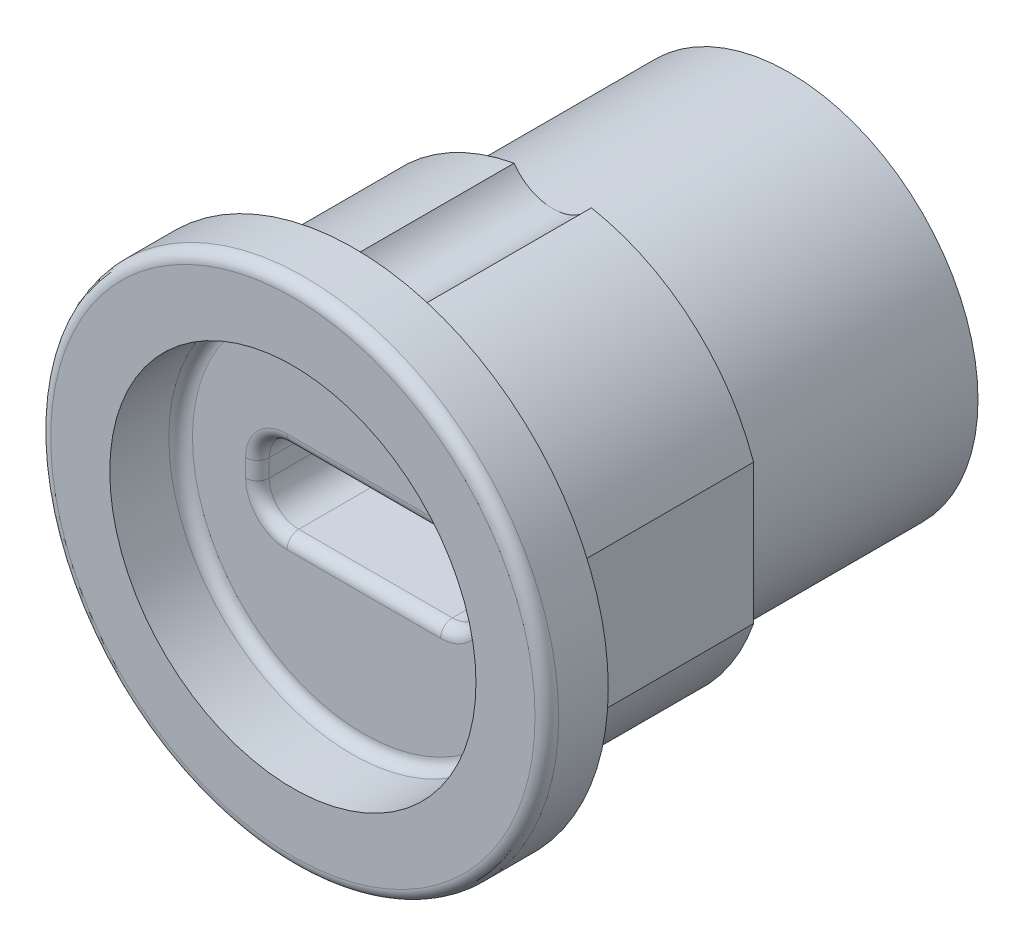
SolidWorks part; units mm, degrees
material "ABS"
ref_plane "Front Plane" through (0, 0, 0) normal (0, 0, 1) x (1, 0, 0)
ref_plane "Top Plane" through (0, 0, 0) normal (0, 1, 0) x (1, 0, 0)
ref_plane "Right Plane" through (0, 0, 0) normal (1, 0, 0) x (0, 0, -1)
sketch "Sketch1" plane through (0, 0, 0) normal (0, 0, 1) x (1, 0, 0)
  circle A0 centre (0, 0) radius 9
  dimension "D1" = 18
extrude "Boss-Extrude1" add sketch "Sketch1" against normal blind 18.4
sketch "Sketch2" plane through (0, 0, 0) normal (0, 0, 1) x (1, 0, 0)
  circle A0 centre (0, 0) radius 10.75
  dimension "D1" = 21.5
extrude "Boss-Extrude2" add sketch "Sketch2" along normal blind 2.6
sketch "Sketch3" plane through (0, 0, 2.6) normal (0, 0, 1) x (1, 0, 0)
  circle A0 centre (0, 0) radius 7.75
  dimension "D1" = 15.5
extrude "Cut-Extrude1" cut sketch "Sketch3" against normal blind 3
sketch "Sketch4" plane through (0, 0, -18.4) normal (0, 0, -1) x (-1, 0, 0)
  circle A0 centre (0, 0) radius 8
  circle A1 centre (0, 0) radius 9 construction
  circle A2 centre (0, 0) radius 9
  dimension "D1" = 16
extrude "Cut-Extrude2" cut sketch "Sketch4" against normal blind 10
sketch "Sketch5" plane through (0, 0, -8.4) normal (0, 0, -1) x (-1, 0, 0)
  line L0 (-8.5, 2.958) -> (-8.5, -2.958)
  line L1 (8.5, 2.958) -> (8.5, -2.958)
  circle A0 centre (0, 0) radius 9 construction
  arc A1 (-8.5, 2.958) -> (-8.5, -2.958) centre (0, 0) ccw
  arc A2 (8.5, 2.958) -> (-8.5, 2.958) centre (0, 0) ccw construction
  arc A3 (-8.5, -2.958) -> (8.5, -2.958) centre (0, 0) ccw construction
  arc A4 (8.5, -2.958) -> (8.5, 2.958) centre (0, 0) ccw
  arc A5 (-1.6363, 8.85) -> (1.6363, 8.85) centre (0, 10) ccw
  circle A6 centre (0, 0) radius 8 construction
  circle A7 centre (0, 0) radius 9 construction
  arc A8 (-1.6363, 8.85) -> (1.6363, 8.85) centre (0, 0) cw
  point P7 (-8.5, 0)
  point P9 (8.5, 0)
  point P11 (0, 8)
  dimension "D2" = 2
  dimension "D1" = 17
extrude "Cut-Extrude3" cut sketch "Sketch5" against normal up to surface (8.4 mm away) up to face at (9, 0, 0)
sketch "Sketch6" plane through (0, 0, 0) normal (0, 0, 1) x (1, 0, 0)
  line L1 (-3.25, 1.625) -> (3.25, 1.625)
  line L2 (-3.25, -1.625) -> (3.25, -1.625)
  line L7 (-4.5, -0.375) -> (-4.5, 0.375)
  line L8 (4.5, -0.375) -> (4.5, 0.375)
  arc A2 (-3.25, 1.625) -> (-4.5, 0.375) centre (-3.25, 0.375) ccw
  arc A3 (-4.5, -0.375) -> (-3.25, -1.625) centre (-3.25, -0.375) ccw
  arc A4 (3.25, -1.625) -> (4.5, -0.375) centre (3.25, -0.375) ccw
  arc A5 (4.5, 0.375) -> (3.25, 1.625) centre (3.25, 0.375) ccw
  point P0 (-3.222, -1.625)
  point P1 (4.5, 0)
  point P3 (0, 0)
  point P4 (0, 1.625)
  point P8 (0, 0)
  point P10 (0, 0)
  point P26 (0, 0)
  point P27 (0, 0)
  point P28 (0, 0)
  point P29 (0, 0)
  point P30 (0, 0)
  point P31 (0, 0)
  point P32 (0, 0)
  point P33 (-3.4616, 0.5866)
  dimension "D3" = 1.25
  dimension "D1" = 3.25
  dimension "D4" = 9
extrude "Cut-Extrude4" cut sketch "Sketch6" against normal through all
fillet "Fillet1" radius 0.5 10 edges at (4.1339, 1.2589, -0.4) (4.5, 0, -0.4) (4.1339, -1.2589, -0.4) (0, -1.625, -0.4) (-4.1339, -1.2589, -0.4) (-4.5, 0, -0.4) (-4.1339, 1.2589, -0.4) (10.75, 0, 2.6) (7.75, 0, -0.4) (0, 1.625, -0.4)
